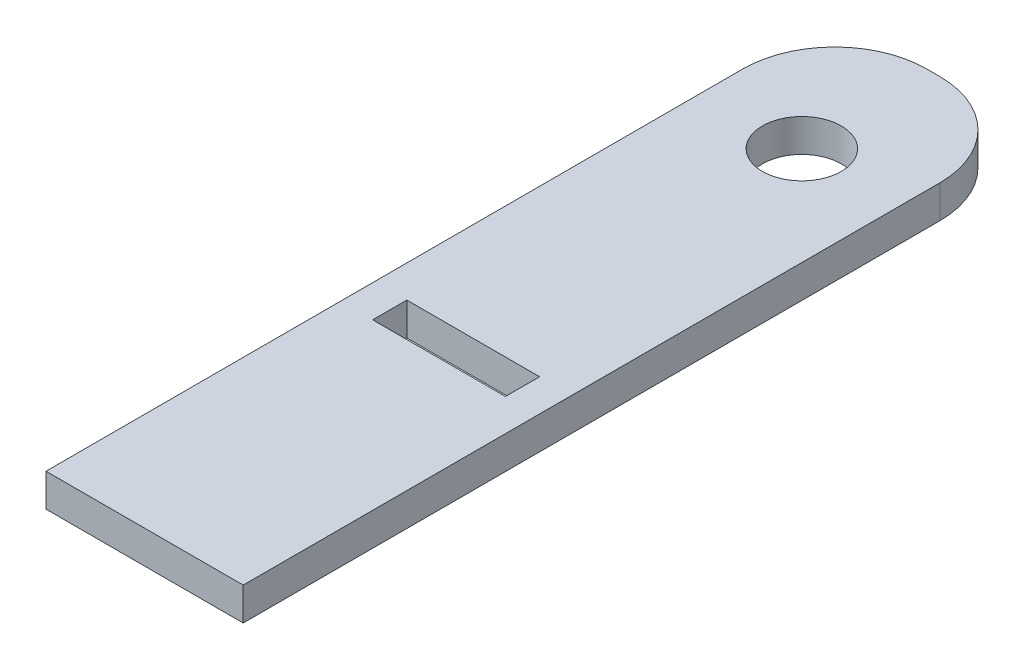
SolidWorks part; units mm, degrees
ref_plane "Front Plane" through (0, 0, 0) normal (0, 0, 1) x (1, 0, 0)
ref_plane "Top Plane" through (0, 0, 0) normal (0, 1, 0) x (1, 0, 0)
ref_plane "Right Plane" through (0, 0, 0) normal (1, 0, 0) x (0, 0, -1)
sketch "Sketch1" plane through (0, 0, 0) normal (0, 1, 0) x (1, 0, 0)
  line L1 (-9.525, 38.1) -> (9.525, 38.1)
  line L2 (-9.525, 38.1) -> (-9.525, -38.1)
  line L3 (-9.525, -38.1) -> (9.525, -38.1)
  line L4 (9.525, 38.1) -> (9.525, -38.1)
  line L5 (-6.4135, -6.35) -> (6.4135, -6.35)
  line L6 (-6.4135, -6.35) -> (-6.4135, -9.652)
  line L7 (-6.4135, -9.652) -> (6.4135, -9.652)
  line L8 (6.4135, -6.35) -> (6.4135, -9.652)
  circle A0 centre (0, 25.4) radius 3.81
  point P4 (9.525, 0)
  point P5 (0, 38.1)
  point P13 (0, -9.652)
  dimension "D3" = 7.62
  dimension "D1" = 19.05
  dimension "D2" = 76.2
  dimension "D4" = 12.7
  dimension "D5" = 12.827
  dimension "D6" = 3.302
  dimension "D7" = 6.35
extrude "Boss-Extrude1" add sketch "Sketch1" along normal blind 3.175
fillet "Fillet1" radius 8.89 1 edges at (9.525, 1.5875, -38.1)
fillet "Fillet2" radius 8.89 1 edges at (-9.525, 1.5875, -38.1)
